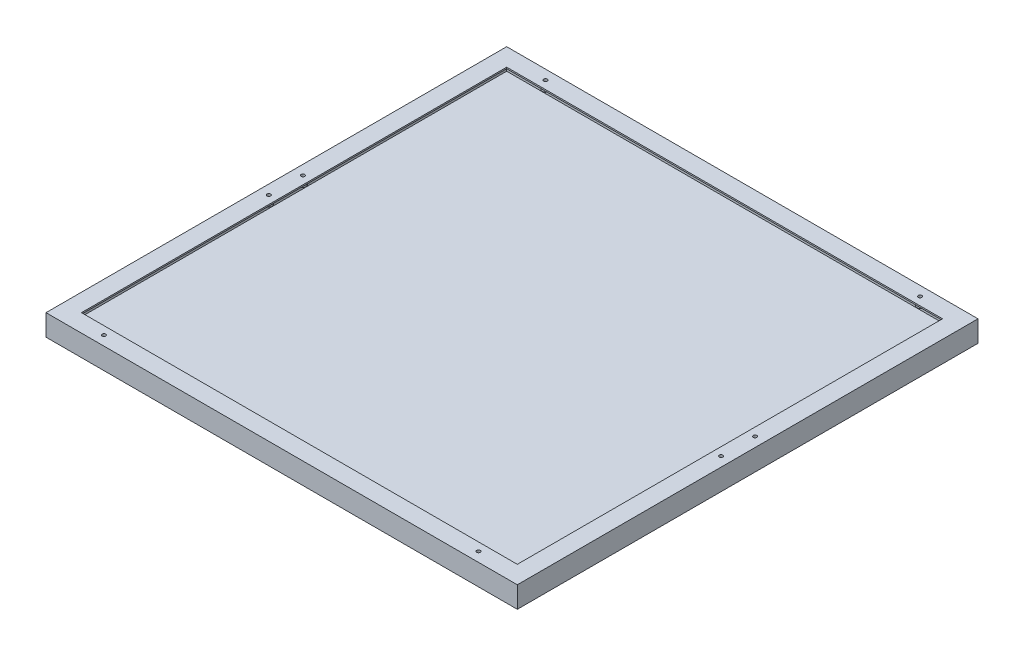
SolidWorks part; units mm, degrees
material "6061-T6 (SS)"
ref_plane "Front" through (0, 0, 0) normal (0, 0, 1) x (1, 0, 0)
ref_plane "Top" through (0, 0, 0) normal (0, 1, 0) x (1, 0, 0)
ref_plane "Right" through (0, 0, 0) normal (1, 0, 0) x (0, 0, -1)
sketch "Sketch1" plane through (0, 0, 0) normal (0, 1, 0) x (1, 0, 0)
  line L1 (0, 0) -> (665, 0)
  line L2 (0, 0) -> (0, 650)
  line L3 (0, 650) -> (665, 650)
  line L4 (665, 0) -> (665, 650)
  dimension "D1" = 665
  dimension "D2" = 650
extrude "Boss-Extrude1" add sketch "Sketch1" against normal blind 30
hole_wizard "#8 (0.199) Diameter Hole1" positions "Sketch3" profile "Sketch2" hole size "#8" standard "ANSI Inch"
sketch "Sketch3" plane through (0, 0, 0) normal (0, 1, 0) x (1, 0, 0)
  line L0 (0, 650) -> (0, 0) construction
  line L1 (0, 0) -> (665, 0) construction
  line L3 (332.5, 650) -> (332.5, 0) construction
  line L4 (665, 650) -> (0, 650) construction
  line L6 (0, 325) -> (665, 325) construction
  line L7 (665, 0) -> (665, 650) construction
  point P10 (68.25, 13.5)
  point P12 (13.5, 301)
  point P43 (596.75, 13.5)
  point P44 (651.5, 301)
  point P47 (651.5, 349)
  point P48 (596.75, 636.5)
  point P49 (68.25, 636.5)
  point P50 (13.5, 349)
  dimension "D1" = 13.5
  dimension "D4" = 301
  dimension "D5" = 13.5
  dimension "D6" = 68.25
sketch "Sketch2" plane through (68.25, 0, -13.5) normal (1, 0, 0) x (0, 0, 1)
  line L0 (0, 0) -> (0, 9.65)
  line L1 (0, 9.65) -> (2.5273, 9.65)
  line L2 (2.5273, 9.65) -> (2.5273, 0)
  line L5 (2.5273, 0) -> (0, 0)
  line L10 (0, 9.65) -> (-2.5273, 9.65) construction
  line L11 (0, -6.35) -> (0, 107.95) construction
  dimension "Hole Dia." = 5.0546
  dimension "Hole Depth" = 9.65
  dimension "Drill Angle" = 180
sketch "Sketch4" plane through (0, 0, 0) normal (0, 1, 0) x (1, 0, 0)
  line L0 (0, 650) -> (0, 0) construction
  line L1 (25, 625) -> (640, 625)
  line L2 (25, 625) -> (25, 25)
  line L3 (25, 25) -> (640, 25)
  line L4 (640, 625) -> (640, 25)
  line L5 (665, 650) -> (0, 650) construction
  line L6 (665, 0) -> (665, 650) construction
  line L7 (0, 0) -> (665, 0) construction
  dimension "D1" = 25
  dimension "D2" = 25
  dimension "D3" = 25
  dimension "D4" = 25
extrude "Cut-Extrude1" cut sketch "Sketch4" against normal blind 20
shell "Shell" thickness 2
